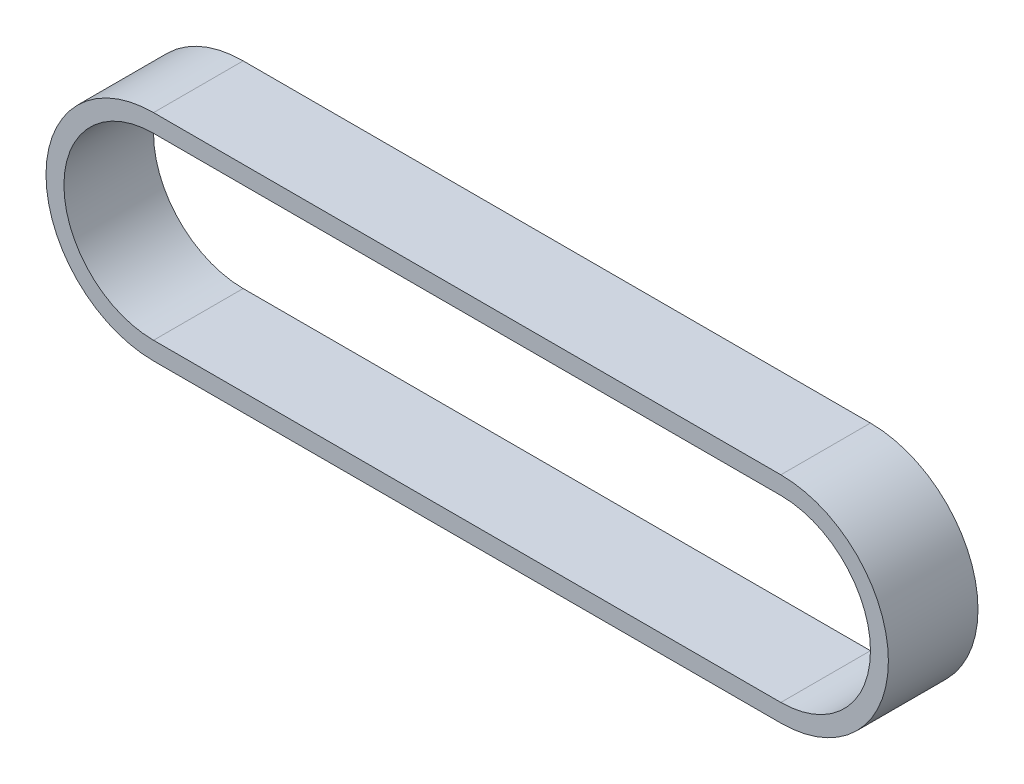
SolidWorks part; units mm, degrees
material "BUTYL"
ref_plane "Front Plane" through (0, 0, 0) normal (0, 0, 1) x (1, 0, 0)
ref_plane "Top Plane" through (0, 0, 0) normal (0, 1, 0) x (1, 0, 0)
ref_plane "Right Plane" through (0, 0, 0) normal (1, 0, 0) x (0, 0, -1)
sketch "Sketch1" plane through (0, 0, 0) normal (0, 0, 1) x (1, 0, 0)
  line L0 (0, 0) -> (35, 0) construction
  line L1 (0, 5) -> (35, 5)
  line L2 (0, -5) -> (35, -5)
  line L3 (0, 0) -> (35, 0) construction
  line L4 (0, 6) -> (35, 6)
  line L5 (0, -6) -> (35, -6)
  arc A0 (0, 5) -> (0, -5) centre (0, 0) ccw
  arc A1 (35, -5) -> (35, 5) centre (35, 0) ccw
  arc A2 (0, 6) -> (0, -6) centre (0, 0) ccw
  arc A3 (35, -6) -> (35, 6) centre (35, 0) ccw
  point P3 (17.5, 0)
  point P8 (17.5, 0)
  dimension "D2" = 5
  dimension "D3" = 1
  dimension "D1" = 35
extrude "Boss-Extrude1" add sketch "Sketch1" along normal blind 5
